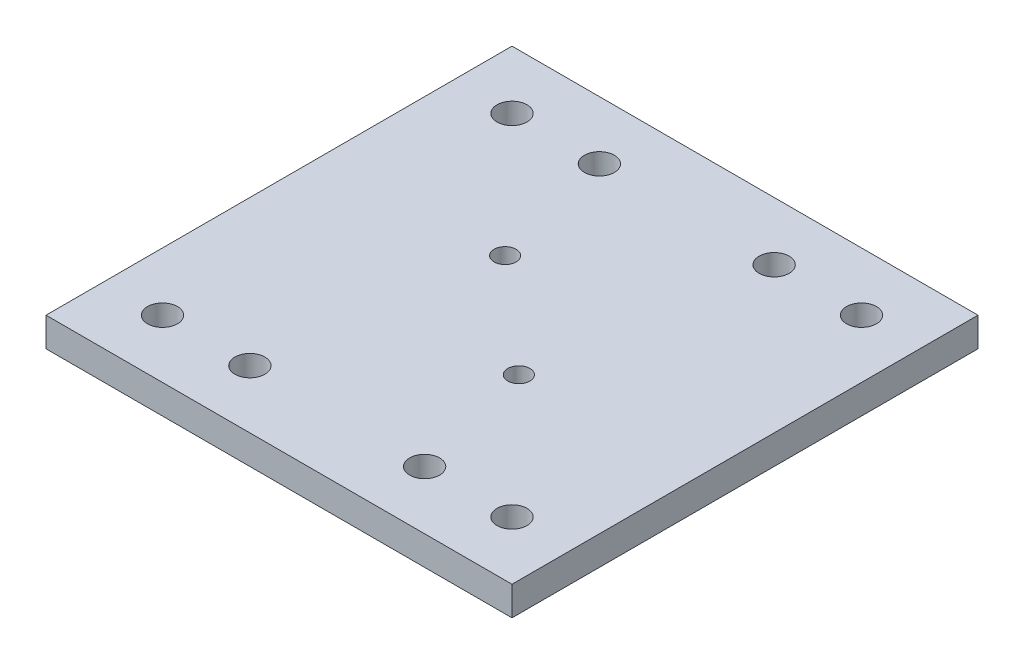
SolidWorks part; units mm, degrees
material "Copper"
ref_plane "Front Plane" through (0, 0, 0) normal (0, 0, 1) x (1, 0, 0)
ref_plane "Top Plane" through (0, 0, 0) normal (0, 1, 0) x (1, 0, 0)
ref_plane "Right Plane" through (0, 0, 0) normal (1, 0, 0) x (0, 0, -1)
sketch "Sketch1" plane through (0, 0, 0) normal (0, 1, 0) x (1, 0, 0)
  line L1 (-25.4, 25.4) -> (25.4, 25.4)
  line L2 (-25.4, 25.4) -> (-25.4, -25.4)
  line L3 (-25.4, -25.4) -> (25.4, -25.4)
  line L4 (25.4, 25.4) -> (25.4, -25.4)
  line L5 (-25.4, 25.4) -> (25.4, -25.4) construction
  line L6 (-25.4, -25.4) -> (25.4, 25.4) construction
  point P0 (0, 0)
  dimension "D1" = 50.8
  dimension "D2" = 50.8
extrude "Boss-Extrude1" add sketch "Sketch1" along normal blind 3.175
hole_wizard "M2 Clearance Hole1" positions "Sketch2" profile "Sketch3" hole size "M2" standard "ANSI Metric" end condition through all
sketch "Sketch2" plane through (0, 3.175, 0) normal (0, 1, 0) x (1, 0, 0)
  line L1 (-6, 5.25) -> (6, 5.25)
  line L2 (-6, 5.25) -> (-6, -5.25)
  line L3 (-6, -5.25) -> (6, -5.25)
  line L4 (6, 5.25) -> (6, -5.25)
  line L5 (-6, 5.25) -> (6, -5.25) construction
  line L6 (-6, -5.25) -> (6, 5.25) construction
  point P2 (6, -5.25)
  point P51 (-6, 5.25)
  dimension "D1" = 12
  dimension "D2" = 10.5
sketch "Sketch3" plane through (6, 3.175, 5.25) normal (1, 0, 0) x (0, 0, 1)
  line L0 (0, 0) -> (0, 3.175)
  line L1 (0, 3.175) -> (1.2, 3.175)
  line L2 (1.2, 3.175) -> (1.2, 0)
  line L5 (1.2, 0) -> (0, 0)
  line L11 (0, -6.35) -> (0, 107.95) construction
  dimension "Thru Hole Dia." = 2.4
  dimension "Thru Hole Depth" = 3.175
hole_wizard "#4 Clearance Hole1" positions "Sketch4" profile "Sketch5" hole size "#4" standard "ANSI Inch" end condition through all
sketch "Sketch4" plane through (0, 3.175, 0) normal (0, 1, 0) x (1, 0, 0)
  line L1 (19.05, 19.05) -> (-19.05, 19.05)
  line L2 (19.05, 19.05) -> (19.05, -19.05)
  line L3 (19.05, -19.05) -> (-19.05, -19.05)
  line L4 (-19.05, 19.05) -> (-19.05, -19.05)
  line L5 (19.05, 19.05) -> (-19.05, -19.05) construction
  line L6 (19.05, -19.05) -> (-19.05, 19.05) construction
  point P2 (-19.05, -19.05)
  point P115 (19.05, 19.05)
  point P116 (19.05, -19.05)
  point P117 (-19.05, 19.05)
  dimension "D1" = 38.1
  dimension "D2" = 38.1
sketch "Sketch5" plane through (-19.05, 3.175, 19.05) normal (1, 0, 0) x (0, 0, 1)
  line L0 (0, 0) -> (0, 3.175)
  line L1 (0, 3.175) -> (1.6319, 3.175)
  line L2 (1.6319, 3.175) -> (1.6319, 0)
  line L5 (1.6319, 0) -> (0, 0)
  line L11 (0, -6.35) -> (0, 107.95) construction
  dimension "Thru Hole Dia." = 3.2639
  dimension "Thru Hole Depth" = 3.175
hole_wizard "#4 Clearance Hole2" positions "Sketch6" profile "Sketch7" hole size "#4" standard "ANSI Inch" end condition through all
sketch "Sketch6" plane through (-33.5042, 3.175, -53.7367) normal (0, 1, 0) x (1, 0, 0)
  point P0 (23.9792, -34.6867)
  point P3 (43.0292, -34.6867)
  point P6 (43.0292, -72.7867)
  point P9 (23.9792, -72.7867)
sketch "Sketch7" plane through (-9.525, 3.175, -19.05) normal (1, 0, 0) x (0, 0, 1)
  line L0 (0, 0) -> (0, 3.175)
  line L1 (0, 3.175) -> (1.6319, 3.175)
  line L2 (1.6319, 3.175) -> (1.6319, 0)
  line L3 (1.6319, 0) -> (0, 0)
  line L4 (0, -6.35) -> (0, 107.95) construction
  dimension "Thru Hole Dia." = 3.2639
  dimension "Thru Hole Depth" = 3.175
